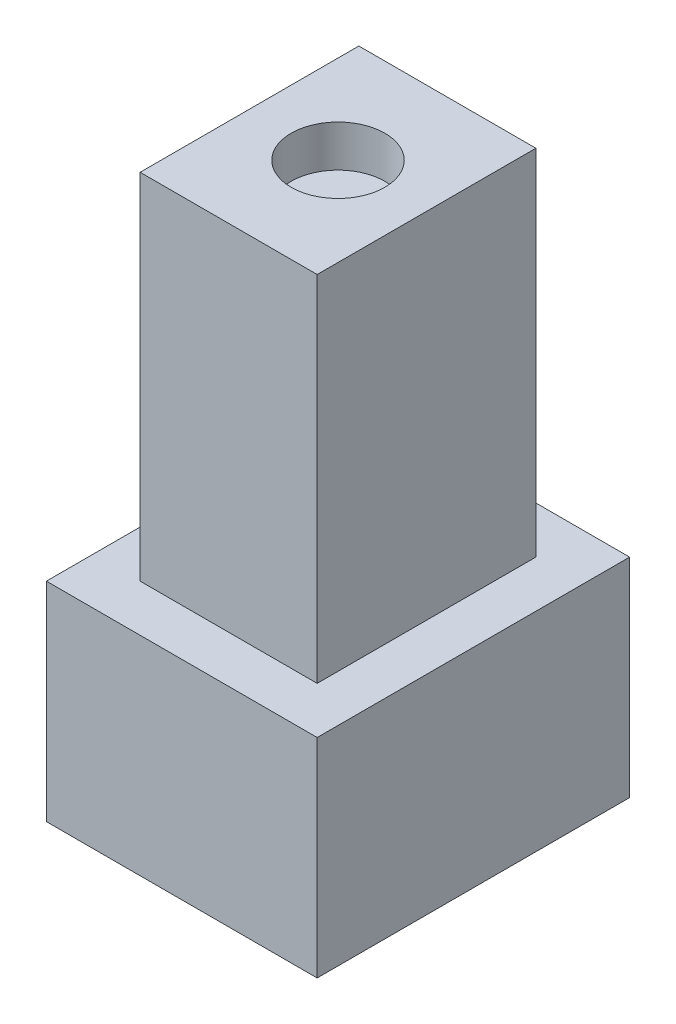
SolidWorks part; units mm, degrees
ref_plane "Front Plane" through (0, 0, 0) normal (0, 0, 1) x (1, 0, 0)
ref_plane "Top Plane" through (0, 0, 0) normal (0, 1, 0) x (1, 0, 0)
ref_plane "Right Plane" through (0, 0, 0) normal (1, 0, 0) x (0, 0, -1)
sketch "Sketch1" plane through (0, 0, 0) normal (0, 1, 0) x (1, 0, 0)
  line L1 (0, 0) -> (13, 0)
  line L2 (0, 0) -> (0, 15)
  line L3 (0, 15) -> (13, 15)
  line L4 (13, 0) -> (13, 15)
  dimension "D1" = 15
  dimension "D2" = 13
extrude "Boss-Extrude1" add sketch "Sketch1" along normal blind 10
sketch "Sketch2" plane through (0, 10, 0) normal (0, 1, 0) x (1, 0, 0)
  line L8 (2.25, 12.75) -> (2.25, 2.25)
  line L9 (2.25, 2.25) -> (10.75, 2.25)
  line L10 (10.75, 2.25) -> (10.75, 12.75)
  line L11 (10.75, 12.75) -> (2.25, 12.75)
  line L12 (2.25, 12.75) -> (2.25, 2.25)
  line L13 (2.25, 2.25) -> (10.75, 2.25)
  line L14 (10.75, 2.25) -> (10.75, 12.75)
  line L15 (10.75, 12.75) -> (2.25, 12.75)
  dimension "D1" = 2.25
extrude "Boss-Extrude2" add sketch "Sketch2" along normal blind 17 contours L12 L13 L14 L15
sketch "Sketch3" plane through (0, 27, 0) normal (0, 1, 0) x (1, 0, 0)
  line L0 (2.25, 2.25) -> (10.75, 2.25) construction
  line L1 (10.75, 2.25) -> (10.75, 12.75) construction
  circle A0 centre (6.5, 7.5) radius 2.25
  dimension "D1" = 5.25
  dimension "D2" = 4.25
  dimension "D3" = 4.5
extrude "Cut-Extrude1" cut sketch "Sketch3" against normal blind 2 contours A0
